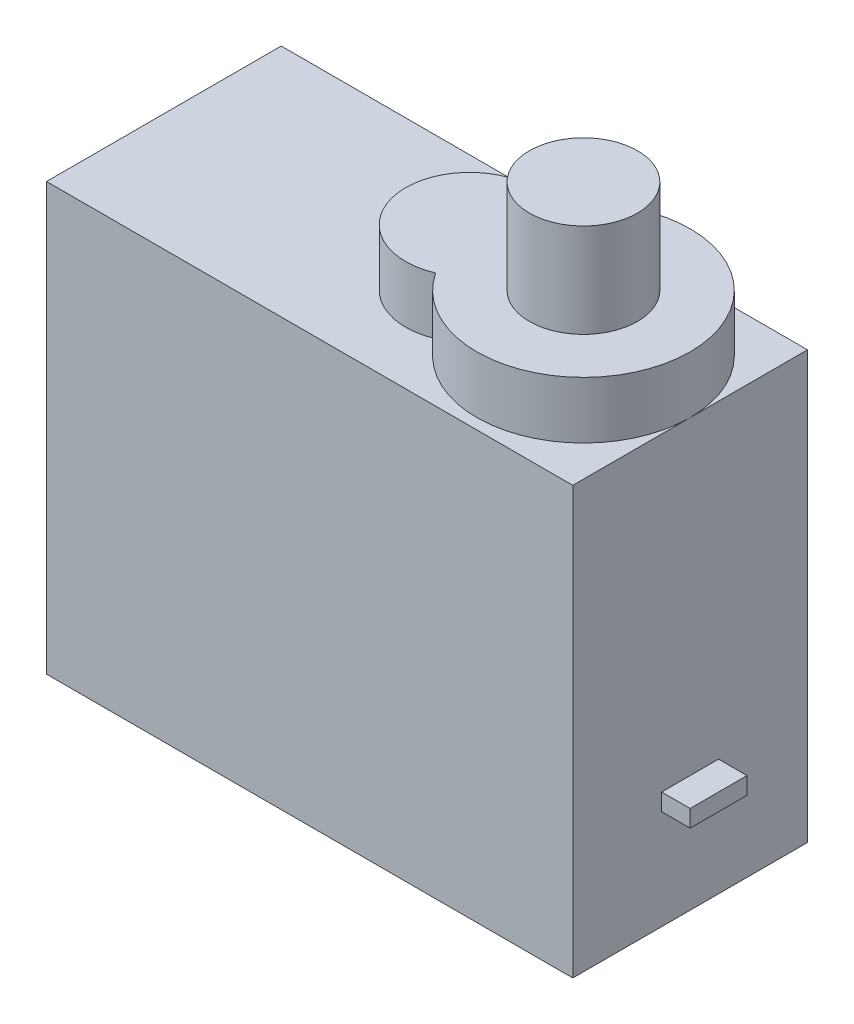
SolidWorks part; units mm, degrees
ref_plane "Front" through (0, 0, 0) normal (0, 0, 1) x (1, 0, 0)
ref_plane "Top" through (0, 0, 0) normal (0, 1, 0) x (1, 0, 0)
ref_plane "Right" through (0, 0, 0) normal (1, 0, 0) x (0, 0, -1)
sketch "草图1" plane through (0, 0, 0) normal (0, 1, 0) x (1, 0, 0)
  line L1 (9.25, -4.125) -> (-9.25, -4.125)
  line L2 (9.25, -4.125) -> (9.25, 4.125)
  line L3 (9.25, 4.125) -> (-9.25, 4.125)
  line L4 (-9.25, -4.125) -> (-9.25, 4.125)
  line L5 (9.25, -4.125) -> (-9.25, 4.125) construction
  line L6 (9.25, 4.125) -> (-9.25, -4.125) construction
  point P0 (0, 0)
  dimension "D1" = 18.5
  dimension "D2" = 8.25
extrude "凸台-拉伸1" add sketch "草图1" along normal blind 15
sketch "草图2" plane through (0, 15, 0) normal (0, 1, 0) x (1, 0, 0)
  line L0 (-14.8322, 0) -> (13.7625, 0) construction
  line L1 (9.25, -4.125) -> (9.25, 4.125) construction
  circle A0 centre (5.5, 0) radius 3.75
  dimension "D2" = 7.5
  dimension "D1" = 3.75
extrude "凸台-拉伸2" add sketch "草图2" along normal blind 2
sketch "草图3" plane through (0, 15, 0) normal (0, 1, 0) x (1, 0, 0)
  line L0 (-11.0431, 0) -> (11.1033, 0) construction
  circle A0 centre (1.5, 0) radius 2.25
  circle A1 centre (5.5, 0) radius 3.75 construction
  dimension "D2" = 4.5
  dimension "D1" = 4
extrude "凸台-拉伸3" add sketch "草图3" along normal blind 2
sketch "草图4" plane through (0, 17, 0) normal (0, 1, 0) x (1, 0, 0)
  circle A0 centre (5.5, 0) radius 1.9
  dimension "D1" = 3.8
extrude "凸台-拉伸4" add sketch "草图4" along normal blind 3.3
sketch "草图5" plane through (9.25, 0, 0) normal (1, 0, 0) x (0, 0, -1)
  line L0 (0, -4.1819) -> (0, 9.9009) construction
  line L1 (-4.125, 0) -> (4.125, 0) construction
  line L2 (1, 3.5) -> (-1, 3.5)
  line L3 (1, 3.5) -> (1, 4.1)
  line L4 (1, 4.1) -> (-1, 4.1)
  line L5 (-1, 3.5) -> (-1, 4.1)
  line L6 (1, 3.5) -> (-1, 4.1) construction
  line L7 (1, 4.1) -> (-1, 3.5) construction
  point P3 (0, 3.8)
  dimension "D1" = 0.6
  dimension "D2" = 2
  dimension "D3" = 3.8
extrude "凸台-拉伸5" add sketch "草图5" along normal blind 1
